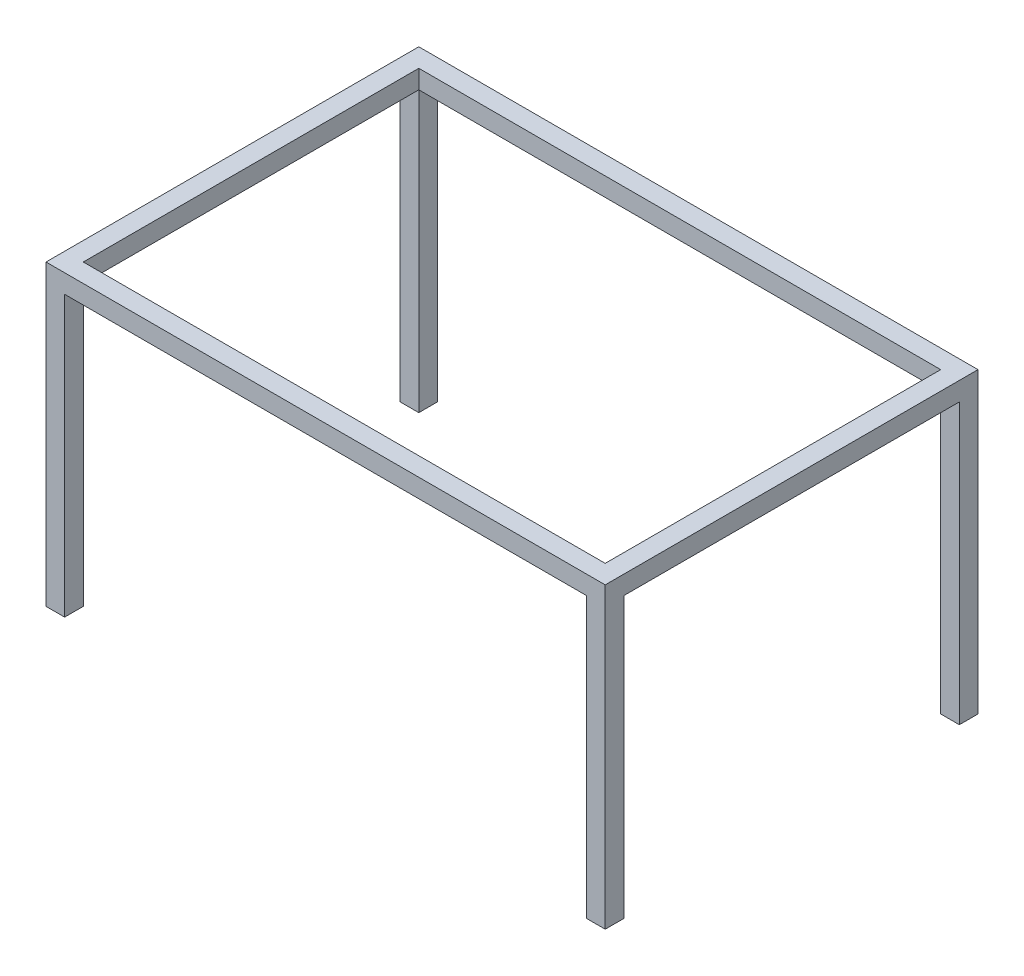
SolidWorks part; units mm, degrees
ref_plane "Alzado" through (0, 0, 0) normal (0, 0, 1) x (1, 0, 0)
ref_plane "Planta" through (0, 0, 0) normal (0, 1, 0) x (1, 0, 0)
ref_plane "Vista lateral" through (0, 0, 0) normal (1, 0, 0) x (0, 0, -1)
sketch "Croquis1" plane through (0, 0, 0) normal (0, 1, 0) x (1, 0, 0)
  line L0 (-1400, 900) -> (1400, 900)
  line L1 (-1500, -1000) -> (1500, -1000)
  line L2 (-1500, -1000) -> (-1500, 1000)
  line L3 (-1500, 1000) -> (1500, 1000)
  line L4 (1500, -1000) -> (1500, 1000)
  line L7 (1400, -900) -> (1400, 900)
  line L8 (-1400, -900) -> (1400, -900)
  line L9 (-1400, -900) -> (-1400, 900)
  point P0 (0, 0)
  dimension "D1" = 2000
  dimension "D2" = 3000
  dimension "D3" = 100
extrude "Saliente-Extruir1" add sketch "Croquis1" along normal blind 100
sketch "Croquis2" plane through (0, 0, 0) normal (0, -1, 0) x (1, 0, 0)
  line L1 (-1500, 1000) -> (-1400, 1000)
  line L2 (-1500, 1000) -> (-1500, 900)
  line L3 (-1500, 900) -> (-1400, 900)
  line L4 (-1400, 1000) -> (-1400, 900)
  line L5 (-1400, -900) -> (-1500, -900)
  line L6 (-1400, -900) -> (-1400, -1000)
  line L7 (-1400, -1000) -> (-1500, -1000)
  line L8 (-1500, -900) -> (-1500, -1000)
  line L9 (1500, -1000) -> (1400, -1000)
  line L10 (1500, -1000) -> (1500, -900)
  line L11 (1500, -900) -> (1400, -900)
  line L12 (1400, -1000) -> (1400, -900)
  line L13 (1400, 900) -> (1500, 900)
  line L14 (1400, 900) -> (1400, 1000)
  line L15 (1400, 1000) -> (1500, 1000)
  line L16 (1500, 900) -> (1500, 1000)
extrude "Saliente-Extruir2" add sketch "Croquis2" along normal blind 1500
